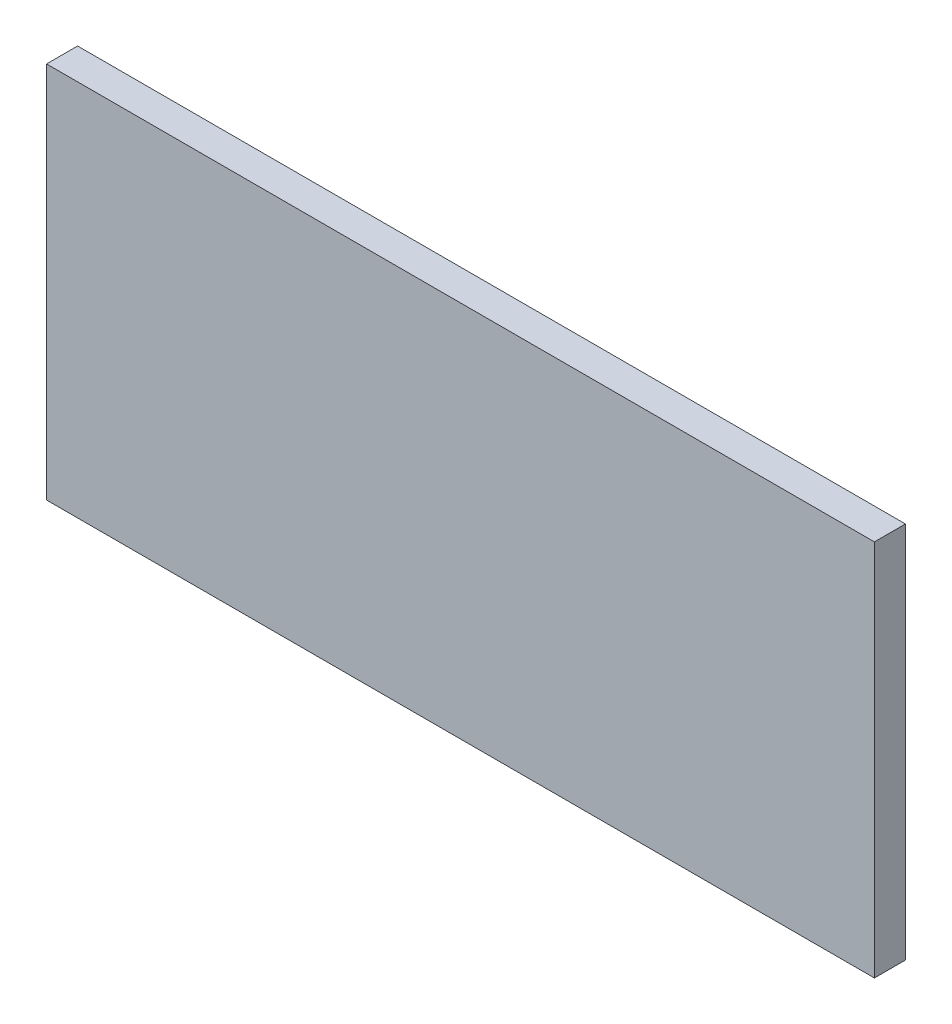
SolidWorks part; units mm, degrees
ref_plane "Front Plane" through (0, 0, 0) normal (0, 0, 1) x (1, 0, 0)
ref_plane "Top Plane" through (0, 0, 0) normal (0, 1, 0) x (1, 0, 0)
ref_plane "Right Plane" through (0, 0, 0) normal (1, 0, 0) x (0, 0, -1)
sketch "Sketch1" plane through (0, 0, 0) normal (0, 0, 1) x (1, 0, 0)
  line L1 (0, 0) -> (80, 0)
  line L2 (0, 0) -> (0, 36.5)
  line L3 (0, 36.5) -> (80, 36.5)
  line L4 (80, 0) -> (80, 36.5)
sketch "Sketch2" plane through (0, 0, 0) normal (0, 1, 0) x (1, 0, 0)
  line L1 (0, 3) -> (80, 3)
  line L2 (0, 3) -> (0, 0)
  line L3 (0, 0) -> (80, 0)
  line L4 (80, 3) -> (80, 0)
extrude "Boss-Extrude1" add sketch "Sketch1" against normal up to vertex (3 mm away) up to point (0, 0, -3)
